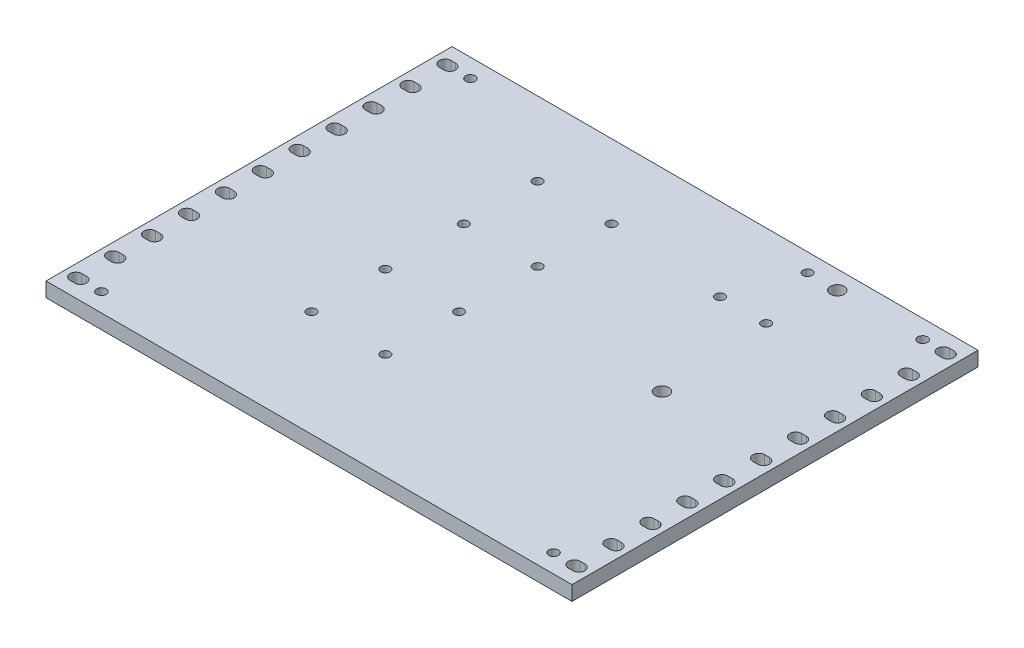
SolidWorks part; units mm, degrees
other "Markup1"
sketch "Sketch3" plane through (330.2, 10, 0) normal (0.0623, 0.8147, 0.5765) x (0.9973, -0.0285, -0.0676)
material "Polyurethane Foam Rigid"
ref_plane "Front Plane" through (0, 0, 0) normal (0, 0, 1) x (1, 0, 0)
ref_plane "Top Plane" through (0, 0, 0) normal (0, 1, 0) x (1, 0, 0)
ref_plane "Right Plane" through (0, 0, 0) normal (1, 0, 0) x (0, 0, -1)
sketch "Sketch1" plane through (0, 0, 0) normal (0, 1, 0) x (1, 0, 0)
  line L1 (0, 0) -> (361.95, 0)
  line L2 (0, 0) -> (0, 279.4)
  line L3 (0, 279.4) -> (361.95, 279.4)
  line L4 (361.95, 0) -> (361.95, 279.4)
  line L5 (38.1, 0) -> (292.1, 0)
  dimension "D1" = 361.95
  dimension "D2" = 279.4
extrude "Boss-Extrude1" add sketch "Sketch1" along normal blind 10
sketch "Sketch2" plane through (0, 10, 0) normal (0, 1, 0) x (1, 0, 0)
  line L0 (352.425, 279.4) -> (352.425, 0)
  line L1 (0, 279.4) -> (361.95, 279.4) construction
  line L2 (0, 0) -> (361.95, 0) construction
  line L3 (350.8375, 266.7) -> (354.0125, 266.7) construction
  line L5 (350.8375, 270.764) -> (354.0125, 270.764)
  line L6 (350.8375, 262.636) -> (354.0125, 262.636)
  line L7 (352.425, 266.7) -> (352.425, 241.3) construction
  line L8 (180.975, 279.4) -> (180.975, 0) construction
  line L13 (350.8375, 241.3) -> (354.0125, 241.3) construction
  line L14 (350.8375, 245.364) -> (354.0125, 245.364)
  line L15 (350.8375, 237.236) -> (354.0125, 237.236)
  line L16 (350.8375, 215.9) -> (354.0125, 215.9) construction
  line L17 (350.8375, 219.964) -> (354.0125, 219.964)
  line L18 (350.8375, 211.836) -> (354.0125, 211.836)
  line L19 (350.8375, 190.5) -> (354.0125, 190.5) construction
  line L20 (350.8375, 194.564) -> (354.0125, 194.564)
  line L21 (350.8375, 186.436) -> (354.0125, 186.436)
  line L22 (350.8375, 165.1) -> (354.0125, 165.1) construction
  line L23 (350.8375, 169.164) -> (354.0125, 169.164)
  line L24 (350.8375, 161.036) -> (354.0125, 161.036)
  line L25 (350.8375, 139.7) -> (354.0125, 139.7) construction
  line L26 (350.8375, 143.764) -> (354.0125, 143.764)
  line L27 (350.8375, 135.636) -> (354.0125, 135.636)
  line L28 (350.8375, 114.3) -> (354.0125, 114.3) construction
  line L29 (350.8375, 118.364) -> (354.0125, 118.364)
  line L30 (350.8375, 110.236) -> (354.0125, 110.236)
  line L31 (350.8375, 88.9) -> (354.0125, 88.9) construction
  line L32 (350.8375, 92.964) -> (354.0125, 92.964)
  line L33 (350.8375, 84.836) -> (354.0125, 84.836)
  line L34 (350.8375, 63.5) -> (354.0125, 63.5) construction
  line L35 (350.8375, 67.564) -> (354.0125, 67.564)
  line L36 (350.8375, 59.436) -> (354.0125, 59.436)
  line L37 (350.8375, 38.1) -> (354.0125, 38.1) construction
  line L38 (350.8375, 42.164) -> (354.0125, 42.164)
  line L39 (350.8375, 34.036) -> (354.0125, 34.036)
  line L40 (350.8375, 12.7) -> (354.0125, 12.7) construction
  line L41 (350.8375, 16.764) -> (354.0125, 16.764)
  line L42 (350.8375, 8.636) -> (354.0125, 8.636)
  line L43 (11.1125, 266.7) -> (7.9375, 266.7) construction
  line L44 (11.1125, 270.764) -> (7.9375, 270.764)
  line L45 (11.1125, 262.636) -> (7.9375, 262.636)
  line L46 (11.1125, 12.7) -> (7.9375, 12.7) construction
  line L47 (11.1125, 16.764) -> (7.9375, 16.764)
  line L48 (11.1125, 8.636) -> (7.9375, 8.636)
  line L49 (11.1125, 38.1) -> (7.9375, 38.1) construction
  line L50 (11.1125, 42.164) -> (7.9375, 42.164)
  line L51 (11.1125, 34.036) -> (7.9375, 34.036)
  line L52 (11.1125, 63.5) -> (7.9375, 63.5) construction
  line L53 (11.1125, 67.564) -> (7.9375, 67.564)
  line L54 (11.1125, 59.436) -> (7.9375, 59.436)
  line L55 (11.1125, 88.9) -> (7.9375, 88.9) construction
  line L56 (11.1125, 92.964) -> (7.9375, 92.964)
  line L57 (11.1125, 84.836) -> (7.9375, 84.836)
  line L58 (11.1125, 114.3) -> (7.9375, 114.3) construction
  line L59 (11.1125, 118.364) -> (7.9375, 118.364)
  line L60 (11.1125, 110.236) -> (7.9375, 110.236)
  line L61 (11.1125, 139.7) -> (7.9375, 139.7) construction
  line L62 (11.1125, 143.764) -> (7.9375, 143.764)
  line L63 (11.1125, 135.636) -> (7.9375, 135.636)
  line L64 (11.1125, 165.1) -> (7.9375, 165.1) construction
  line L65 (11.1125, 169.164) -> (7.9375, 169.164)
  line L66 (11.1125, 161.036) -> (7.9375, 161.036)
  line L67 (11.1125, 190.5) -> (7.9375, 190.5) construction
  line L68 (11.1125, 194.564) -> (7.9375, 194.564)
  line L69 (11.1125, 186.436) -> (7.9375, 186.436)
  line L70 (11.1125, 215.9) -> (7.9375, 215.9) construction
  line L71 (11.1125, 219.964) -> (7.9375, 219.964)
  line L72 (11.1125, 211.836) -> (7.9375, 211.836)
  line L73 (11.1125, 241.3) -> (7.9375, 241.3) construction
  line L74 (11.1125, 245.364) -> (7.9375, 245.364)
  line L75 (11.1125, 237.236) -> (7.9375, 237.236)
  line L76 (361.95, 0) -> (361.95, 279.4) construction
  arc A30 (350.8375, 270.764) -> (350.8375, 262.636) centre (350.8375, 266.7) ccw
  arc A31 (354.0125, 262.636) -> (354.0125, 270.764) centre (354.0125, 266.7) ccw
  arc A45 (350.8375, 245.364) -> (350.8375, 237.236) centre (350.8375, 241.3) ccw
  arc A46 (354.0125, 237.236) -> (354.0125, 245.364) centre (354.0125, 241.3) ccw
  arc A47 (350.8375, 219.964) -> (350.8375, 211.836) centre (350.8375, 215.9) ccw
  arc A48 (354.0125, 211.836) -> (354.0125, 219.964) centre (354.0125, 215.9) ccw
  arc A49 (350.8375, 194.564) -> (350.8375, 186.436) centre (350.8375, 190.5) ccw
  arc A50 (354.0125, 186.436) -> (354.0125, 194.564) centre (354.0125, 190.5) ccw
  arc A51 (350.8375, 169.164) -> (350.8375, 161.036) centre (350.8375, 165.1) ccw
  arc A52 (354.0125, 161.036) -> (354.0125, 169.164) centre (354.0125, 165.1) ccw
  arc A53 (350.8375, 143.764) -> (350.8375, 135.636) centre (350.8375, 139.7) ccw
  arc A54 (354.0125, 135.636) -> (354.0125, 143.764) centre (354.0125, 139.7) ccw
  arc A55 (350.8375, 118.364) -> (350.8375, 110.236) centre (350.8375, 114.3) ccw
  arc A56 (354.0125, 110.236) -> (354.0125, 118.364) centre (354.0125, 114.3) ccw
  arc A57 (350.8375, 92.964) -> (350.8375, 84.836) centre (350.8375, 88.9) ccw
  arc A58 (354.0125, 84.836) -> (354.0125, 92.964) centre (354.0125, 88.9) ccw
  arc A59 (350.8375, 67.564) -> (350.8375, 59.436) centre (350.8375, 63.5) ccw
  arc A60 (354.0125, 59.436) -> (354.0125, 67.564) centre (354.0125, 63.5) ccw
  arc A61 (350.8375, 42.164) -> (350.8375, 34.036) centre (350.8375, 38.1) ccw
  arc A62 (354.0125, 34.036) -> (354.0125, 42.164) centre (354.0125, 38.1) ccw
  arc A63 (350.8375, 16.764) -> (350.8375, 8.636) centre (350.8375, 12.7) ccw
  arc A64 (354.0125, 8.636) -> (354.0125, 16.764) centre (354.0125, 12.7) ccw
  arc A65 (11.1125, 270.764) -> (11.1125, 262.636) centre (11.1125, 266.7) cw
  arc A66 (7.9375, 262.636) -> (7.9375, 270.764) centre (7.9375, 266.7) cw
  arc A67 (11.1125, 16.764) -> (11.1125, 8.636) centre (11.1125, 12.7) cw
  arc A68 (7.9375, 8.636) -> (7.9375, 16.764) centre (7.9375, 12.7) cw
  arc A69 (11.1125, 42.164) -> (11.1125, 34.036) centre (11.1125, 38.1) cw
  arc A70 (7.9375, 34.036) -> (7.9375, 42.164) centre (7.9375, 38.1) cw
  arc A71 (11.1125, 67.564) -> (11.1125, 59.436) centre (11.1125, 63.5) cw
  arc A72 (7.9375, 59.436) -> (7.9375, 67.564) centre (7.9375, 63.5) cw
  arc A73 (11.1125, 92.964) -> (11.1125, 84.836) centre (11.1125, 88.9) cw
  arc A74 (7.9375, 84.836) -> (7.9375, 92.964) centre (7.9375, 88.9) cw
  arc A75 (11.1125, 118.364) -> (11.1125, 110.236) centre (11.1125, 114.3) cw
  arc A76 (7.9375, 110.236) -> (7.9375, 118.364) centre (7.9375, 114.3) cw
  arc A77 (11.1125, 143.764) -> (11.1125, 135.636) centre (11.1125, 139.7) cw
  arc A78 (7.9375, 135.636) -> (7.9375, 143.764) centre (7.9375, 139.7) cw
  arc A79 (11.1125, 169.164) -> (11.1125, 161.036) centre (11.1125, 165.1) cw
  arc A80 (7.9375, 161.036) -> (7.9375, 169.164) centre (7.9375, 165.1) cw
  arc A81 (11.1125, 194.564) -> (11.1125, 186.436) centre (11.1125, 190.5) cw
  arc A82 (7.9375, 186.436) -> (7.9375, 194.564) centre (7.9375, 190.5) cw
  arc A83 (11.1125, 219.964) -> (11.1125, 211.836) centre (11.1125, 215.9) cw
  arc A84 (7.9375, 211.836) -> (7.9375, 219.964) centre (7.9375, 215.9) cw
  arc A85 (11.1125, 245.364) -> (11.1125, 237.236) centre (11.1125, 241.3) cw
  arc A86 (7.9375, 237.236) -> (7.9375, 245.364) centre (7.9375, 241.3) cw
  point P8 (352.425, 266.7)
  point P19 (352.425, 241.3)
  point P26 (352.425, 215.9)
  point P33 (352.425, 190.5)
  point P40 (352.425, 165.1)
  point P49 (352.425, 139.7)
  point P56 (352.425, 114.3)
  point P63 (352.425, 88.9)
  point P70 (352.425, 63.5)
  point P77 (352.425, 38.1)
  point P84 (352.425, 12.7)
  point P90 (9.525, 266.7)
  point P97 (9.525, 12.7)
  point P104 (9.525, 38.1)
  point P111 (9.525, 63.5)
  point P118 (9.525, 88.9)
  point P125 (9.525, 114.3)
  point P132 (9.525, 139.7)
  point P139 (9.525, 165.1)
  point P146 (9.525, 190.5)
  point P153 (9.525, 215.9)
  point P160 (9.525, 241.3)
  dimension "D3" = 3.175
  dimension "D1" = 9.525
  dimension "D2" = 8.128
  dimension "D4" = 12.7
  dimension "D5" = 11
extrude "Cut-Extrude1" cut sketch "Sketch2" against normal through all and the other way through all contours L41 A63 L42 L0 | L42 A64 L41 L0 | L39 A62 L38 L0
sketch "Sketch4" plane through (0, 0, 0) normal (0, -1, 0) x (1, 0, 0)
  line L1 (0, -279.4) -> (361.95, -279.4) construction
  line L2 (361.95, 0) -> (361.95, -279.4) construction
  circle A0 centre (277.8125, -266.7) radius 4.7625
  circle A1 centre (277.8125, -146.05) radius 4.7625
  dimension "D1" = 84.1375
  dimension "D3" = 9.525
  dimension "D2" = 12.7
  dimension "D4" = 120.65
extrude "Cut-Extrude2" cut sketch "Sketch4" against normal through all
sketch "Sketch5" plane through (0, 0, 0) normal (0, -1, 0) x (1, 0, 0)
  line L0 (361.95, 0) -> (361.95, -279.4) construction
  line L1 (0, -279.4) -> (361.95, -279.4) construction
  circle A3 centre (257.175, -266.9441) radius 3.175
  circle A4 centre (273.05, -222.4941) radius 3.175
  circle A5 centre (241.3, -222.4941) radius 3.175
  dimension "D6" = 6.35
  dimension "D1" = 15.875
  dimension "D2" = 88.9
  dimension "D3" = 31.75
  dimension "D4" = 56.9059
  dimension "D5" = 12.4559
extrude "Cut-Extrude3" cut sketch "Sketch5" against normal through all
sketch "Sketch6" plane through (0, 0, 0) normal (0, -1, 0) x (1, 0, 0)
  line L1 (109.697, -228.6) -> (109.697, -73.025) construction
  line L2 (361.95, 0) -> (361.95, -279.4) construction
  line L3 (0, -279.4) -> (361.95, -279.4) construction
  line L4 (160.497, -228.6) -> (160.497, -73.025) construction
  circle A4 centre (109.697, -228.6) radius 3.175
  circle A5 centre (109.697, -177.8) radius 3.175
  circle A6 centre (109.697, -123.825) radius 3.175
  circle A7 centre (109.697, -73.025) radius 3.175
  circle A8 centre (160.497, -228.6) radius 3.175
  circle A9 centre (160.497, -177.8) radius 3.175
  circle A10 centre (160.497, -123.825) radius 3.175
  circle A11 centre (160.497, -73.025) radius 3.175
  point P25 (160.497, -150.8125)
  point P26 (109.697, -150.8125)
  dimension "D1" = 252.253
  dimension "D6" = 6.35
  dimension "D2" = 50.8
  dimension "D3" = 101.6
  dimension "D4" = 50.8
  dimension "D5" = 50.8
  dimension "D7" = 50.8
extrude "Cut-Extrude4" cut sketch "Sketch6" against normal through all
sketch "Sketch7" plane through (0, 0, 0) normal (0, -1, 0) x (1, 0, 0)
  line L0 (361.95, 0) -> (361.95, -279.4) construction
  line L1 (0, 0) -> (361.95, 0) construction
  line L2 (0, 0) -> (0, -279.4) construction
  circle A4 centre (25.4, -266.7) radius 3.302
  circle A5 centre (336.55, -266.7) radius 3.302
  circle A6 centre (336.55, -12.7) radius 3.302
  circle A7 centre (25.4, -12.7) radius 3.302
  dimension "D1" = 25.4
  dimension "D3" = 25.4
  dimension "D2" = 12.7
extrude "Cut-Extrude5" cut sketch "Sketch7" against normal through all
